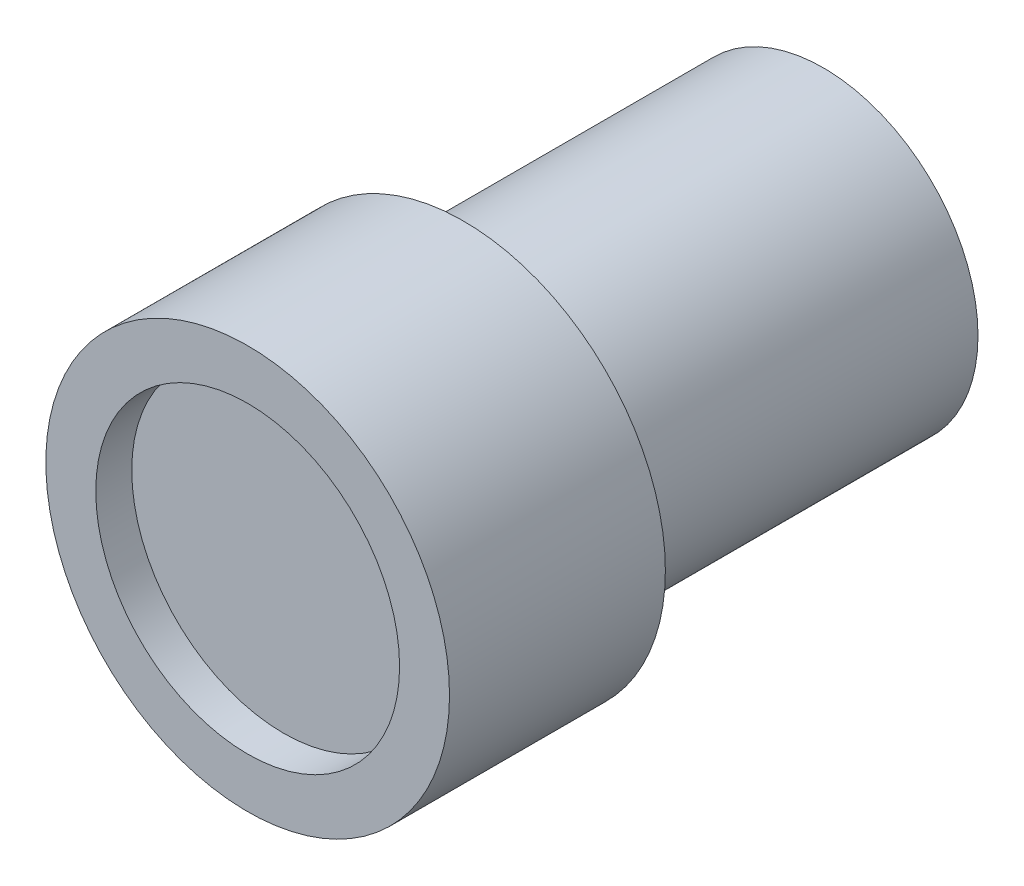
SolidWorks part; units mm, degrees
ref_plane "Front Plane" through (0, 0, 0) normal (0, 0, 1) x (1, 0, 0)
ref_plane "Top Plane" through (0, 0, 0) normal (0, 1, 0) x (1, 0, 0)
ref_plane "Right Plane" through (0, 0, 0) normal (1, 0, 0) x (0, 0, -1)
sketch "Sketch1" plane through (0, 0, 0) normal (0, 0, 1) x (1, 0, 0)
  circle A0 centre (0, 0) radius 5.461
extrude "Extrude1" add sketch "Sketch1" along normal blind 12.7
sketch "Sketch2" plane through (0, 0, 12.7) normal (0, 0, 1) x (1, 0, 0)
  circle A0 centre (0, 0) radius 7.1251
extrude "Extrude2" add sketch "Sketch2" along normal blind 7.62
sketch "Sketch3" plane through (0, 0, 20.32) normal (0, 0, 1) x (1, 0, 0)
  circle A0 centre (0, 0) radius 5.3624
extrude "Extrude3" cut sketch "Sketch3" against normal blind 1.27
